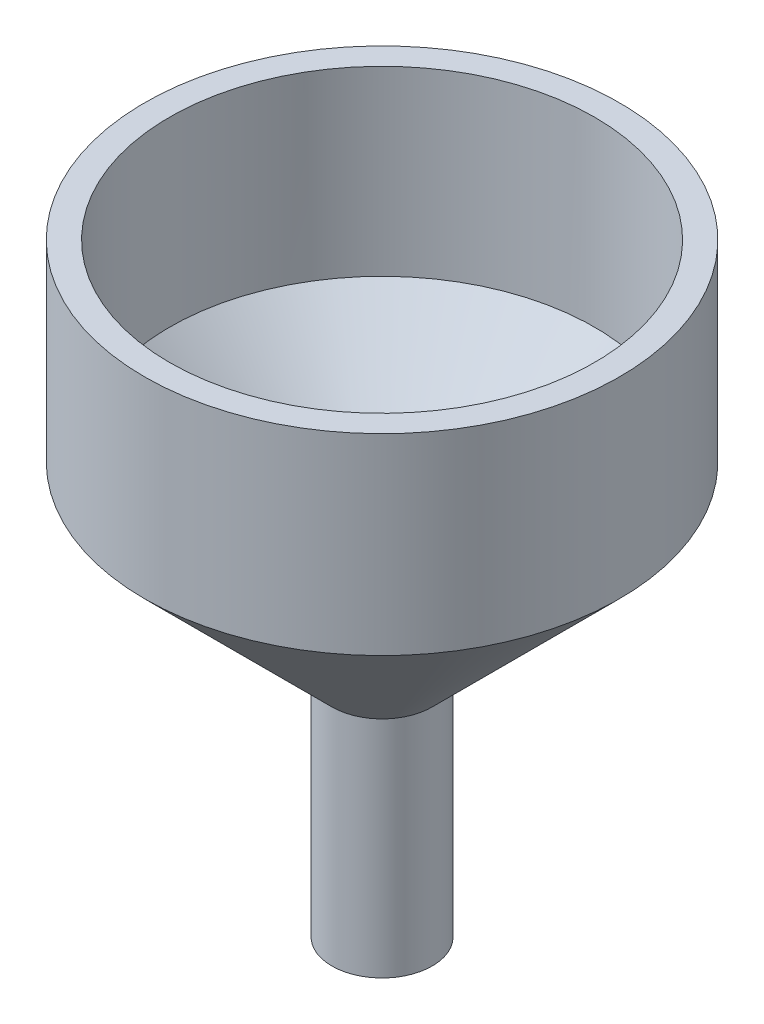
SolidWorks part; units mm, degrees
ref_plane "Alzado" through (0, 0, 0) normal (0, 0, 1) x (1, 0, 0)
ref_plane "Planta" through (0, 0, 0) normal (0, 1, 0) x (1, 0, 0)
ref_plane "Vista lateral" through (0, 0, 0) normal (1, 0, 0) x (0, 0, -1)
sketch "Croquis1" plane through (0, 0, 0) normal (1, 0, 0) x (0, 0, -1)
  line L0 (0, 53.7163) -> (0, -67.3705)
  line L1 (0, -67.3705) -> (10.0675, -67.3705)
  line L2 (10.0675, -67.3705) -> (10.0675, -22.3765)
  line L3 (10.0675, -22.3765) -> (47.6177, 15.1736)
  line L4 (47.6177, 15.1736) -> (47.6177, 53.7163)
  line L5 (47.6177, 53.7163) -> (0, 53.7163)
revolve "Revolución1" add sketch "Croquis1" angle 360 about L0
shell "Vaciado1" thickness 5
